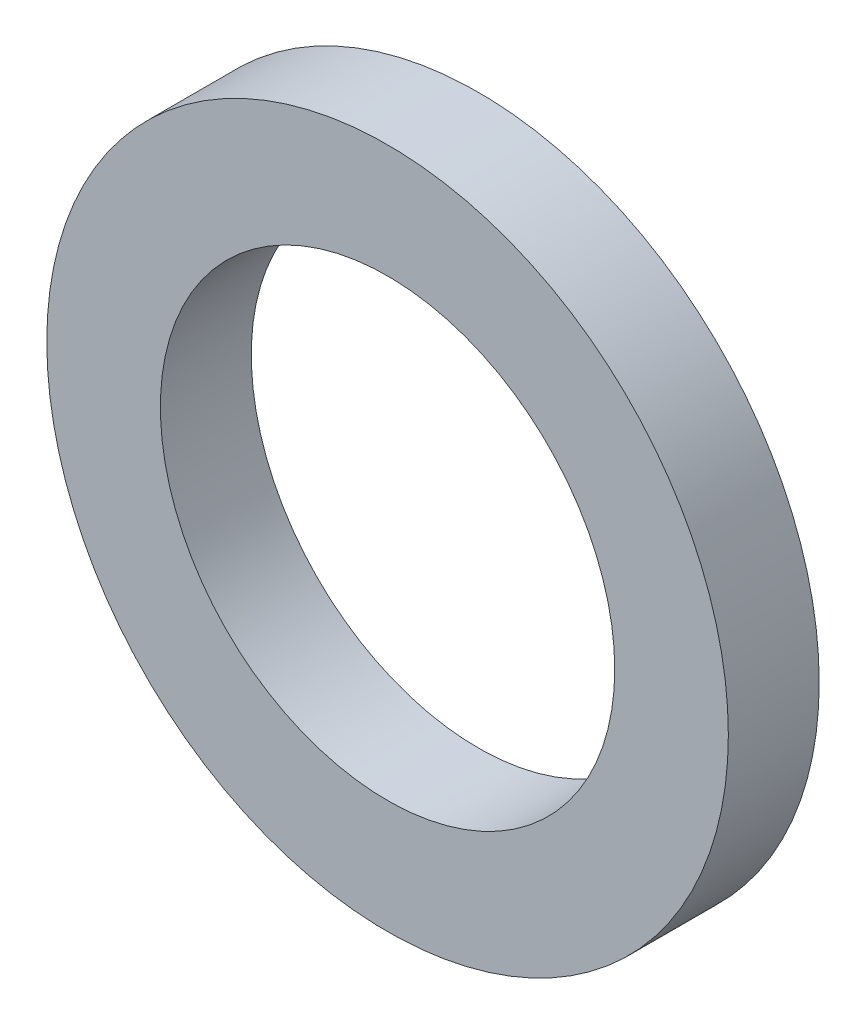
SolidWorks part; units mm, degrees
ref_plane "Front Plane" through (0, 0, 0) normal (0, 0, 1) x (1, 0, 0)
ref_plane "Top Plane" through (0, 0, 0) normal (0, 1, 0) x (1, 0, 0)
ref_plane "Right Plane" through (0, 0, 0) normal (1, 0, 0) x (0, 0, -1)
sketch "Croquis1" plane through (0, 0, 0) normal (0, 0, 1) x (1, 0, 0)
  circle A0 centre (0, 0) radius 2
  circle A1 centre (0, 0) radius 3
  dimension "D1" = 6
  dimension "D2" = 4
extrude "Saliente-Extruir1" add sketch "Croquis1" along normal blind 0.8
